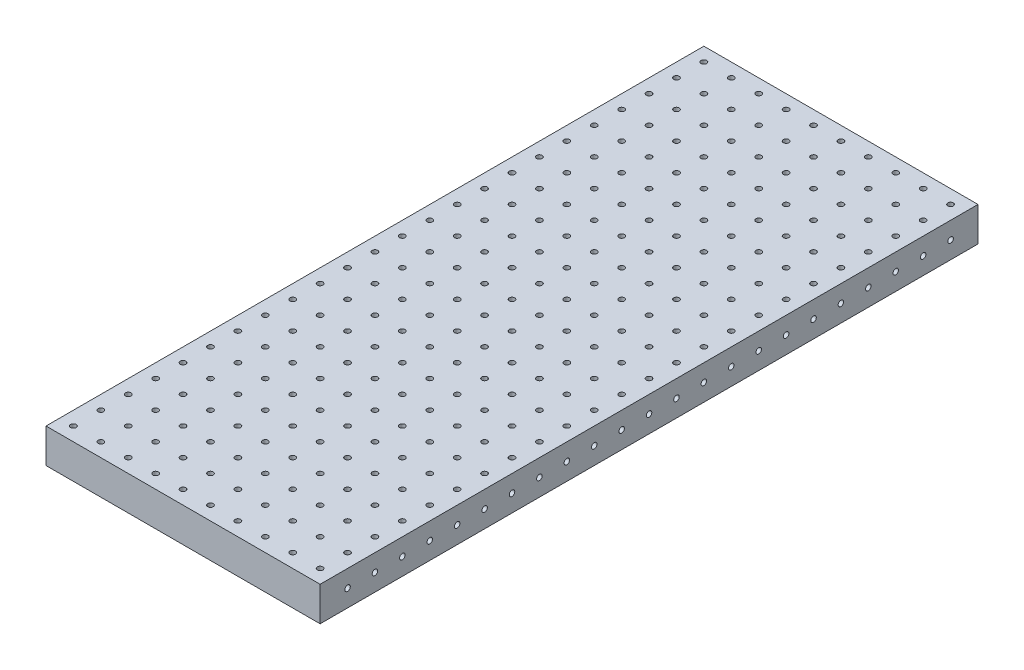
SolidWorks part; units mm, degrees
ref_plane "Front Plane" through (0, 0, 0) normal (0, 0, 1) x (1, 0, 0)
ref_plane "Top Plane" through (0, 0, 0) normal (0, 1, 0) x (1, 0, 0)
ref_plane "Right Plane" through (0, 0, 0) normal (1, 0, 0) x (0, 0, -1)
sketch "Sketch1" plane through (0, 0, 0) normal (0, 1, 0) x (1, 0, 0)
  line L1 (0, 0) -> (254, 0)
  line L2 (0, 0) -> (0, 609.6)
  line L3 (0, 609.6) -> (254, 609.6)
  line L4 (254, 0) -> (254, 609.6)
  dimension "D1" = 609.6
  dimension "D2" = 254
extrude "Boss-Extrude1" add sketch "Sketch1" along normal blind 31.75
hole_wizard "1/4-20 Tapped Hole1" positions "Sketch3" profile "Sketch2" tap size "1/4-20" standard "Ansi Inch" end condition through all
sketch "Sketch3" plane through (0, 31.75, 0) normal (0, 1, 0) x (-1, 0, 0)
  point P0 (-12.7, -12.7)
sketch "Sketch2" plane through (12.7, 31.75, -12.7) normal (1, 0, 0) x (0, 0, 1)
  line L0 (0, 0) -> (0, 31.75)
  line L1 (0, 31.75) -> (2.5527, 31.75)
  line L2 (2.5527, 31.75) -> (2.5527, 0)
  line L5 (2.5527, 0) -> (0, 0)
  line L11 (0, -6.35) -> (0, 107.95) construction
  dimension "Thru Tap Drill Dia." = 5.1054
  dimension "Thru Tap Drill Depth" = 31.75
cosmetic thread "Hole Thread1" parameters "D2"=6.35
pattern_linear "LPattern1" count 24 spacing 25.4 along (0, 0, -1) count 10 spacing 25.4 along (1, 0, 0) of "1/4-20 Tapped Hole1"
hole_wizard "1/4-20 Tapped Hole2" positions "Sketch7" profile "Sketch6" tap size "1/4-20" standard "Ansi Inch"
sketch "Sketch7" plane through (254, 0, 0) normal (1, 0, 0) x (0, 0, -1)
  line L0 (0, 31.75) -> (0, 0) construction
  line L1 (0, 0) -> (609.6, 0) construction
  point P0 (25.4, 15.875)
  point P1 (0, 15.875)
  dimension "D1" = 25.4
  dimension "D2" = 15.875
sketch "Sketch6" plane through (254, 15.875, -25.4) normal (0, 1, 0) x (0, 0, -1)
  line L0 (0, 0) -> (0, 33.2838)
  line L1 (0, 33.2838) -> (2.5527, 31.75)
  line L2 (2.5527, 31.75) -> (2.5527, 0)
  line L5 (2.5527, 0) -> (0, 0)
  line L10 (0, 33.2838) -> (-2.5527, 31.75) construction
  line L11 (0, -6.35) -> (0, 107.95) construction
  dimension "Tap Drill Dia." = 5.1054
  dimension "Tap Drill Depth" = 31.75
  dimension "Drill Angle" = 118
cosmetic thread "Hole Thread2" parameters "D1"=25.4, "D2"=6.35
pattern_linear "LPattern2" count 23 spacing 25.4 along (0, 0, -1) of "1/4-20 Tapped Hole2"
hole_wizard "1/4-20 Tapped Hole3" positions "Sketch10" profile "Sketch12" tap size "1/4-20" standard "Ansi Inch"
sketch "Sketch10" plane through (0, 8.8245, -446.0162) normal (-1, 0, 0) x (0, 0, 1)
  line L2 (-163.5838, 22.9255) -> (-163.5838, -8.8245) construction
  line L3 (-163.5838, -8.8245) -> (446.0162, -8.8245) construction
  point P0 (-138.1838, 7.0505)
  dimension "D1" = 25.4
  dimension "D2" = 15.875
sketch "Sketch12" plane through (0, 15.875, -584.2) normal (0, 1, 0) x (0, 0, 1)
  line L0 (0, 0) -> (0, 33.2838)
  line L1 (0, 33.2838) -> (2.5527, 31.75)
  line L2 (2.5527, 31.75) -> (2.5527, 0)
  line L5 (2.5527, 0) -> (0, 0)
  line L10 (0, 33.2838) -> (-2.5527, 31.75) construction
  line L11 (0, -6.35) -> (0, 107.95) construction
  dimension "Tap Drill Dia." = 5.1054
  dimension "Tap Drill Depth" = 31.75
  dimension "Drill Angle" = 118
cosmetic thread "Hole Thread7" parameters "D1"=25.4, "D2"=6.35
pattern_linear "LPattern3" count 23 spacing 25.4 along (0, 0, 1) of "1/4-20 Tapped Hole3"
hole_wizard "1/4-20 Tapped Hole4" positions "Sketch15" profile "Sketch17" tap size "1/4-20" standard "Ansi Inch"
sketch "Sketch15" plane through (914.3191, -1.4159, -609.6) normal (0, 0, -1) x (-1, 0, 0)
  line L2 (660.3191, 33.1659) -> (660.3191, 1.4159) construction
  line L4 (660.3191, 1.4159) -> (914.3191, 1.4159) construction
  point P0 (685.7191, 17.2909)
  dimension "D1" = 25.4
  dimension "D2" = 15.875
sketch "Sketch17" plane through (228.6, 15.875, -609.6) normal (1, 0, 0) x (0, 1, 0)
  line L0 (0, 0) -> (0, 33.2838)
  line L1 (0, 33.2838) -> (2.5527, 31.75)
  line L2 (2.5527, 31.75) -> (2.5527, 0)
  line L5 (2.5527, 0) -> (0, 0)
  line L10 (0, 33.2838) -> (-2.5527, 31.75) construction
  line L11 (0, -6.35) -> (0, 107.95) construction
  dimension "Tap Drill Dia." = 5.1054
  dimension "Tap Drill Depth" = 31.75
  dimension "Drill Angle" = 118
cosmetic thread "Hole Thread4" parameters "D1"=25.4, "D2"=6.35
pattern_linear "LPattern6" count 9 spacing 25.4 along (-1, 0, 0) of "1/4-20 Tapped Hole4"
sketch "Sketch19" plane through (0, 31.75, 0) normal (0, 1, 0) x (1, 0, 0)
  line L0 (127, 0) -> (127, 50000) construction
  line L1 (0, 0) -> (254, 0) construction
  line L2 (254, 609.6) -> (0, 609.6) construction
  point P4 (127, 0)
  point P7 (127, 609.6)
